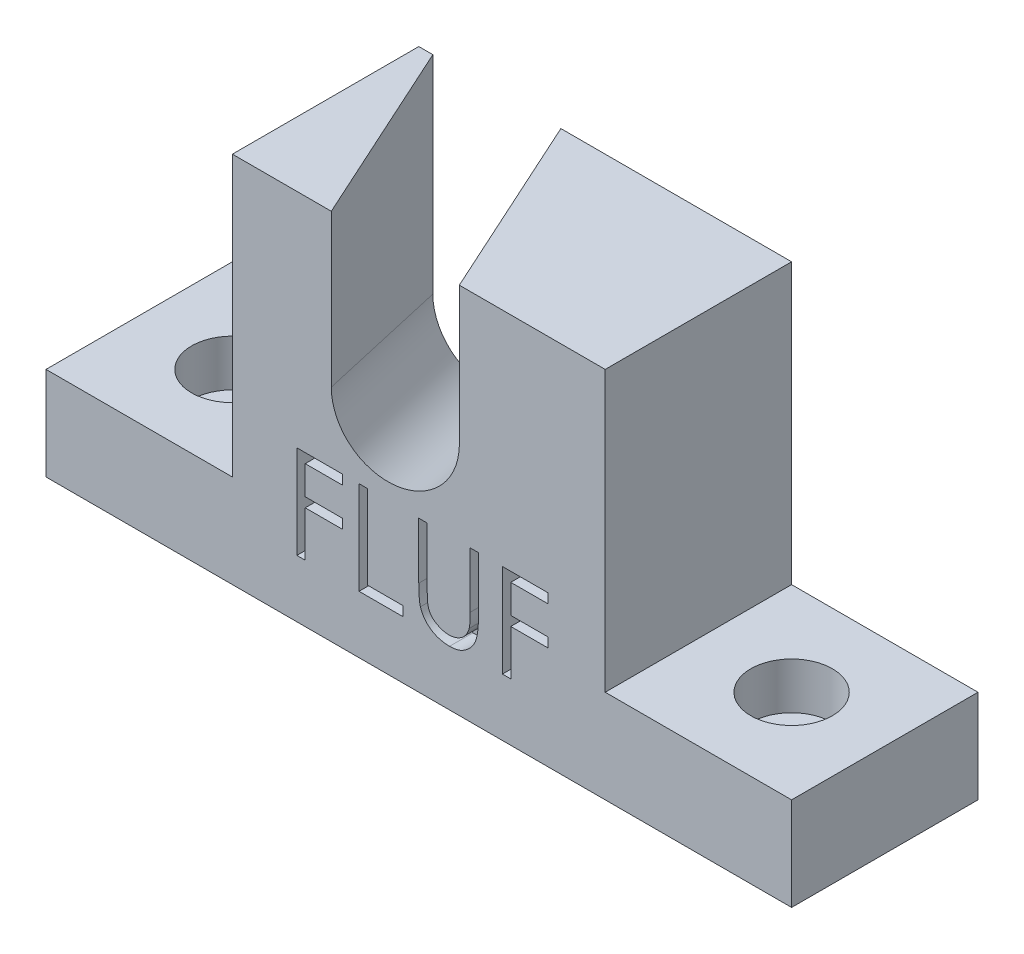
SolidWorks part; units mm, degrees
ref_plane "Front Plane" through (0, 0, 0) normal (0, 0, 1) x (1, 0, 0)
ref_plane "Top Plane" through (0, 0, 0) normal (0, 1, 0) x (1, 0, 0)
ref_plane "Right Plane" through (0, 0, 0) normal (1, 0, 0) x (0, 0, -1)
sketch "Sketch1" plane through (0, 0, 0) normal (0, 0, 1) x (1, 0, 0)
  line L0 (25.4, 12.7) -> (50.8, 12.7)
  line L1 (-50.8, 12.7) -> (-25.4, 12.7)
  line L2 (-50.8, 12.7) -> (-50.8, 0)
  line L3 (-50.8, 0) -> (50.8, 0)
  line L4 (50.8, 12.7) -> (50.8, 0)
  line L5 (-25.4, 50.8) -> (25.4, 50.8)
  line L6 (-25.4, 50.8) -> (-25.4, 12.7)
  line L8 (25.4, 50.8) -> (25.4, 12.7)
  line L9 (0, 0) -> (0, 42.1156) construction
  point P8 (0, 0)
  dimension "D1" = 101.6
  dimension "D2" = 50.8
  dimension "D3" = 12.7
  dimension "D4" = 50.8
extrude "Boss-Extrude1" add sketch "Sketch1" along normal blind 25.4
sketch "Sketch2" plane through (0, 0, 0) normal (0, 1, 0) x (1, 0, 0)
  line L0 (-38.1, 0) -> (-38.1, -25.4) construction
  line L1 (-25.4, 0) -> (-50.8, 0) construction
  line L2 (-25.4, -25.4) -> (-50.8, -25.4) construction
  line L4 (50.8, 0) -> (25.4, 0) construction
  line L5 (38.1, 0) -> (38.1, -25.4) construction
  line L6 (50.8, -25.4) -> (25.4, -25.4) construction
  point P12 (-38.1, -12.7)
  point P13 (38.1, -12.7)
hole_wizard "CBORE for 1/4 Socket Head Cap Screw1" positions "Sketch3" profile "Sketch4" counterbore size "1/4" standard "ANSI Inch" end condition through all
sketch "Sketch3" plane through (0, 12.7, 0) normal (0, 1, 0) x (1, 0, 0)
  point P0 (-38.1, -12.7)
  point P3 (38.1, -12.7)
sketch "Sketch4" plane through (-38.1, 12.7, 12.7) normal (1, 0, 0) x (0, 0, 1)
  line L0 (0, 0) -> (0, 12.7)
  line L1 (0, 12.7) -> (3.3782, 12.7)
  line L3 (3.3782, 12.7) -> (3.3782, 6.35)
  line L4 (3.3782, 6.35) -> (5.5562, 6.35)
  line L5 (5.5562, 6.35) -> (5.5562, 0)
  line L7 (5.5562, 0) -> (0, 0)
  line L11 (0, -6.35) -> (0, 107.95) construction
  dimension "Thru Hole Dia." = 6.7564
  dimension "Thru Hole Depth" = 12.7
  dimension "C'Bore Dia." = 11.1125
  dimension "C'Bore Depth" = 6.35
sketch3d "3DSketch1"
  line L0 (8.6101, 38.6723, 51.3459) -> (-30.0564, 13.6059, -33.5992)
  point P2 (-43.433, 25.9478, 64.5959)
  point P3 (26.6039, 39.1119, -32.1396)
  point P4 (-10.7505, 25.5084, 64.5959)
  point P5 (7.5986, 42.1329, -32.1396)
  point P6 (10.6692, 29.8764, 54.8491)
  point P7 (-4.8854, 30.3551, 60.5472)
  point P8 (-2.5031, 44.1075, -29.0679)
  point P9 (10.4804, 39.5001, -32.2338)
  point P10 (-10.4425, 32.4644, 61.8504)
ref_plane "Plane1" through (8.6101, 38.6723, 51.3459) normal (-0.4001, -0.2594, -0.879) x (-0.9161, 0.0877, 0.3912)
sketch "Sketch6" plane through (8.6101, 38.6723, 51.3459) normal (-0.4001, -0.2594, -0.879) x (-0.9161, 0.0877, 0.3912)
  line L0 (-7.9047, 0.7205) -> (-4.0814, 42.668)
  line L1 (-37.7428, -11.3872) -> (-34.4029, 25.2569) construction
  line L2 (7.9047, -0.7205) -> (11.7281, 41.227)
  line L3 (12.1371, 26.4965) -> (8.7971, -10.1476) construction
  line L4 (-4.0814, 42.668) -> (11.7281, 41.227)
  circle A0 centre (0, 0) radius 7.9375
  point P11 (0, 0)
  point P12 (0, 0)
  dimension "D1" = 15.875
extrude "Cut-Extrude2" cut sketch "Sketch6" along normal through all contours A0 | A0 L2 L4 L0
sketch "Sketch7" plane through (0, 0, 25.4) normal (0, 0, 1) x (1, 0, 0)
  text T0 "FLUF" font "Century Gothic" height 12.7
extrude "Cut-Extrude3" cut sketch "Sketch7" against normal blind 3.175
